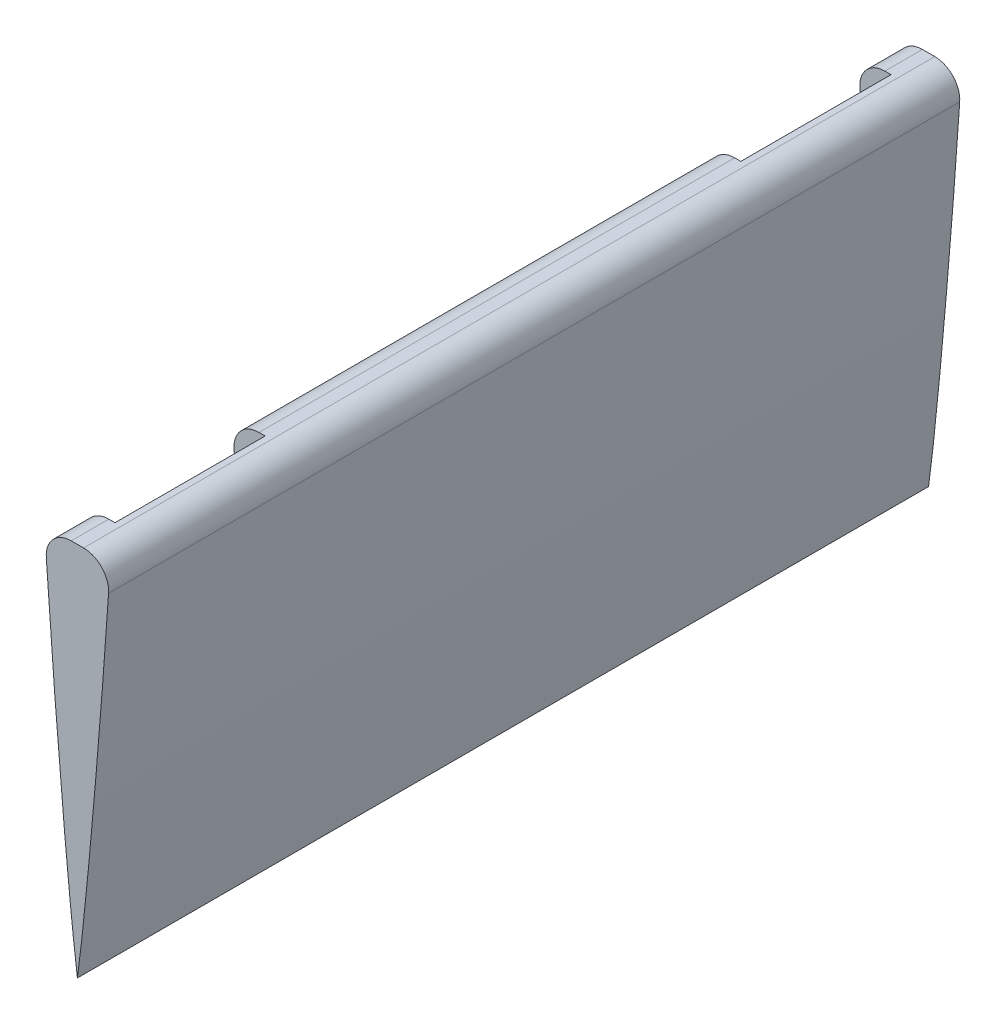
SolidWorks part; units mm, degrees
ref_plane "Front Plane" through (0, 0, 0) normal (0, 0, 1) x (1, 0, 0)
ref_plane "Top Plane" through (0, 0, 0) normal (0, 1, 0) x (1, 0, 0)
ref_plane "Right Plane" through (0, 0, 0) normal (1, 0, 0) x (0, 0, -1)
ref_plane "Plane1" through (0, 0, 35) normal (0, 0, 1) x (1, 0, 0)
sketch "Sketch2" plane through (0, 0, 35) normal (0, 0, 1) x (1, 0, 0)
  line L4 (-0.4933, -665) -> (0.4933, -665)
  line L5 (-0.0463, -694.6522) -> (0, -695)
  arc A0 (-2.4887, -667.136) -> (-0.4933, -665) centre (-0.4933, -667) cw
  arc A1 (2.4887, -667.136) -> (0.4933, -665) centre (0.4933, -667) ccw
  spline S4 degree 3 poles (-2.4887, -667.136) (-2.4254, -668.0646) (-2.249, -670.5823) (-1.9505, -674.5726) (-1.5956, -678.9657) (-1.2543, -682.9383) (-0.9367, -686.4221) (-0.6491, -689.3577) (-0.4032, -691.6945) (-0.2072, -693.3927) (-0.0904, -694.3067) (-0.0463, -694.6522) knots 0.013046 0.013046 0.013046 0.013046 0.030062 0.05919 0.086204 0.110641 0.132086 0.150162 0.164568 0.175046 0.181415 0.181415 0.181415 0.181415
  spline S5 degree 3 poles (0, -695) (0.0155, -694.8841) (0.0773, -694.4229) (0.2061, -693.3925) (0.4037, -691.6946) (0.649, -689.3576) (0.9367, -686.4221) (1.2543, -682.9382) (1.5956, -678.9657) (1.9505, -674.5726) (2.249, -670.5823) (2.4254, -668.0646) (2.4887, -667.136) knots 0.816448 0.816448 0.816448 0.816448 0.818585 0.824954 0.835432 0.849838 0.867914 0.889359 0.913796 0.94081 0.969938 0.986954 0.986954 0.986954 0.986954
  dimension "D2" = 2
extrude "Boss-Extrude1" add sketch "Sketch2" along normal mid plane 68
sketch "Sketch4" plane through (0, 0, 0) normal (-1, 0, 0) x (0, 0, 1)
  line L0 (69, -665) -> (1, -665) construction
  line L1 (66, -665) -> (54, -665)
  line L2 (66, -665) -> (66, -677)
  line L3 (66, -677) -> (54, -677)
  line L4 (54, -665) -> (54, -677)
  line L5 (66, -652.6601) -> (66, -664.6601) construction
  line L6 (16, -665) -> (4, -665)
  line L7 (16, -665) -> (16, -677)
  line L8 (16, -677) -> (4, -677)
  line L9 (4, -665) -> (4, -677)
  line L10 (16, -652.9242) -> (16, -664.9239) construction
  dimension "D1" = 0
  dimension "D2" = 12
  dimension "D3" = 12
  dimension "D4" = 12
  dimension "D5" = 12
  dimension "D6" = 0
  dimension "D7" = 0
extrude "Cut-Extrude1" cut sketch "Sketch4" along normal through all
